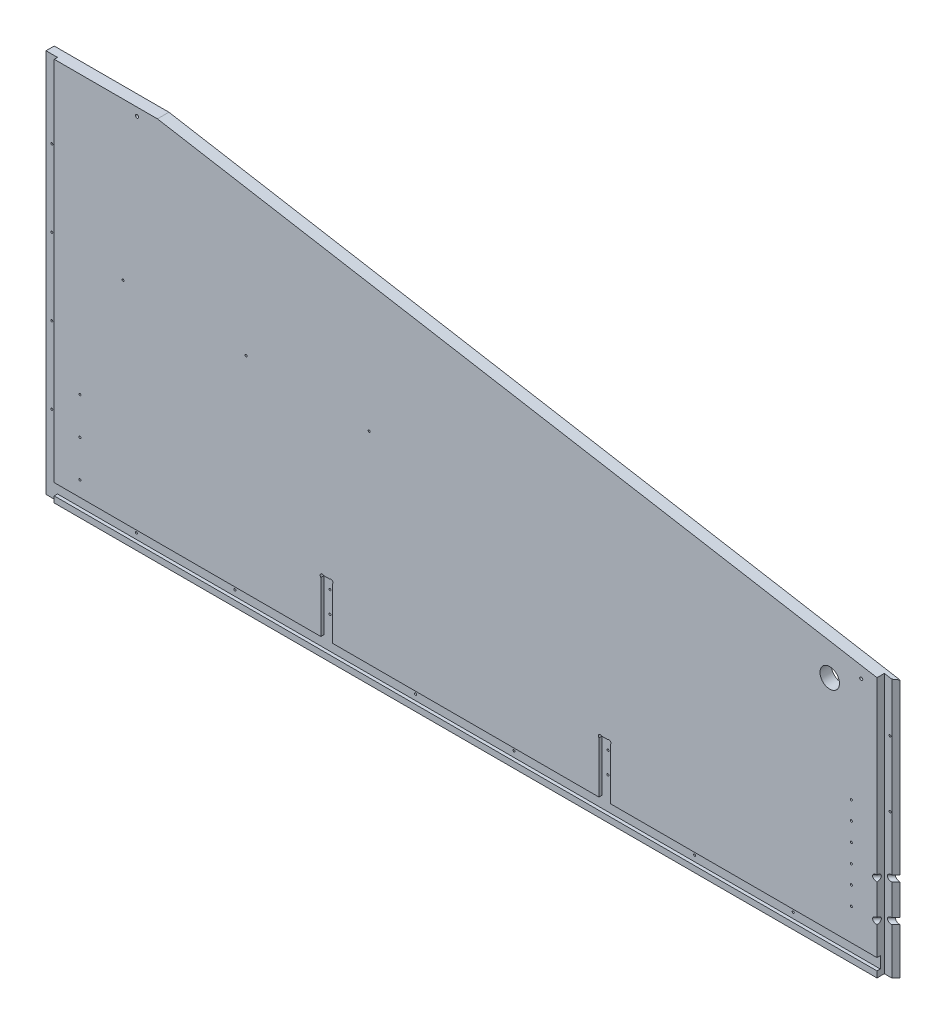
SolidWorks part; units mm, degrees
material "Maple"
ref_plane "Front Plane" through (0, 0, 0) normal (0, 0, 1) x (1, 0, 0)
ref_plane "Top Plane" through (0, 0, 0) normal (0, 1, 0) x (1, 0, 0)
ref_plane "Right Plane" through (0, 0, 0) normal (1, 0, 0) x (0, 0, -1)
sketch "Sketch1" plane through (0, 0, 0) normal (0, 0, 1) x (1, 0, 0)
  line L0 (8932.6508, -5243.5125) -> (10226.1458, -5243.5125)
  line L1 (9086.3208, -4722.0918) -> (10222.9708, -4853.7812)
  line L2 (8914.8708, -6342.0625) -> (10197.5708, -6342.0625)
  line L3 (8914.8708, -5808.6625) -> (10197.5708, -5808.6625)
  line L4 (8919.6333, -5253.0375) -> (10218.2083, -5253.0375)
  line L5 (9134.2633, -4656.1375) -> (9134.2633, -4638.3575)
  line L6 (9091.0833, -4638.3575) -> (9134.2633, -4638.3575)
  line L7 (9091.0833, -4567.2375) -> (9091.0833, -4638.3575)
  line L8 (9134.2633, -4656.1375) -> (9581.3033, -4656.1375)
  line L9 (9091.0833, -4567.2375) -> (9624.4833, -4567.2375)
  line L10 (9581.3033, -4656.1375) -> (9581.3033, -4638.3575)
  line L11 (9581.3033, -4638.3575) -> (9624.4833, -4638.3575)
  line L12 (9624.4833, -4567.2375) -> (9624.4833, -4638.3575)
  line L13 (8932.6508, -5225.7325) -> (9344.9775, -5225.7325)
  line L14 (8932.6508, -5256.2125) -> (8932.6508, -5243.5125)
  line L15 (8911.6958, -5256.2125) -> (8932.6508, -5256.2125)
  line L16 (8914.8708, -4722.0918) -> (9086.3208, -4722.0918)
  line L17 (8911.6958, -4715.5913) -> (8932.6508, -4715.5913)
  line L18 (8914.8708, -6342.0625) -> (8914.8708, -5808.6625)
  line L19 (12082.9917, -4722.0918) -> (10946.3417, -4853.7812)
  line L20 (12236.6617, -5243.5125) -> (10943.1667, -5243.5125)
  line L21 (10951.1042, -5253.0375) -> (12249.6792, -5253.0375)
  line L22 (10838.3917, -5656.2625) -> (11308.2917, -5656.2625)
  line L23 (10838.3917, -5719.7625) -> (11308.2917, -5719.7625)
  line L24 (10838.3917, -5742.5368) -> (11308.2917, -5742.5368)
  line L25 (10806.6417, -6342.0625) -> (11340.0417, -6342.0625)
  line L26 (10803.4667, -6335.7125) -> (11343.2167, -6335.7125)
  line L27 (10803.4667, -6317.9325) -> (11343.2167, -6317.9325)
  line L28 (10943.1667, -5225.7325) -> (11376.4483, -5225.7325)
  line L29 (11506.7292, -4754.5625) -> (10806.6417, -4827.5875)
  line L30 (11506.7292, -4567.2375) -> (11506.7292, -4754.5625)
  line L31 (10806.6417, -4567.2375) -> (10806.6417, -4827.5875)
  line L32 (10806.6417, -4567.2375) -> (11506.7292, -4567.2375)
  line L33 (10235.6708, -6329.3625) -> (10245.1958, -6329.3625)
  line L34 (10245.1958, -6329.3625) -> (10254.7208, -6278.5625)
  line L35 (10302.3458, -6329.3625) -> (10311.8708, -6278.5625)
  line L36 (10302.3458, -6329.3625) -> (10292.8208, -6329.3625)
  line L37 (10245.1958, -5821.3625) -> (10254.7208, -5872.1625)
  line L38 (10235.6708, -5821.3625) -> (10245.1958, -5821.3625)
  line L39 (10292.8208, -5821.3625) -> (10302.3458, -5821.3625)
  line L40 (10302.3458, -5821.3625) -> (10311.8708, -5872.1625)
  line L41 (10235.6708, -5821.3625) -> (10235.6708, -6329.3625)
  line L42 (10254.7208, -5872.1625) -> (10254.7208, -6278.5625)
  line L43 (10311.8708, -5872.1625) -> (10311.8708, -6278.5625)
  line L44 (10292.8208, -5821.3625) -> (10292.8208, -6329.3625)
  line L45 (8932.6508, -5225.7325) -> (8932.6508, -4715.5913)
  line L46 (8911.6958, -4715.5913) -> (8911.6958, -5256.2125)
  line L47 (8914.8708, -5248.275) -> (8914.8708, -4722.0918)
  line L48 (8919.6333, -5253.0375) -> (8914.8708, -5248.275)
  line L49 (8914.8708, -5145.0875) -> (8937.426, -5145.0875)
  line L50 (8914.8708, -5202.2375) -> (8937.426, -5202.2375)
  line L51 (10838.3917, -5656.2625) -> (10838.3917, -5719.7625)
  line L52 (10832.0417, -5736.1868) -> (10856.1717, -5736.1868)
  line L53 (10806.6417, -6342.0625) -> (10806.6417, -5818.7368)
  line L54 (10832.0417, -5649.9125) -> (10856.1717, -5649.9125)
  line L55 (10832.0417, -5726.1125) -> (10856.1717, -5726.1125)
  line L56 (10806.6417, -5818.7368) -> (10833.9015, -5818.7368)
  line L57 (10832.0417, -5806.0442) -> (10851.6815, -5806.0442)
  line L58 (10856.1717, -5801.5541) -> (10856.1717, -5736.1868)
  line L59 (10838.3917, -5814.2467) -> (10838.3917, -5742.5368)
  line L60 (10832.0417, -5806.0442) -> (10832.0417, -5736.1868)
  line L61 (10803.4667, -6317.9325) -> (10803.4667, -6335.7125)
  line L62 (10197.5708, -5808.6625) -> (10197.5708, -6342.0625)
  line L63 (9762.3842, -6348.4125) -> (9762.3842, -5802.3125)
  line L64 (9780.1642, -6348.4125) -> (9762.3842, -6348.4125)
  line L65 (9780.1642, -5802.3125) -> (9780.1642, -6348.4125)
  line L66 (9762.3842, -5802.3125) -> (9780.1642, -5802.3125)
  line L67 (9332.2775, -6348.4125) -> (9332.2775, -5802.3125)
  line L68 (9332.2775, -6348.4125) -> (9350.0575, -6348.4125)
  line L69 (9350.0575, -5802.3125) -> (9350.0575, -6348.4125)
  line L70 (9332.2775, -5802.3125) -> (9350.0575, -5802.3125)
  line L71 (9993.8374, -6061.075) -> (9993.8374, -6045.2418)
  line L72 (9998.5999, -6065.8375) -> (10014.4331, -6065.8375)
  line L73 (9998.5999, -6084.8875) -> (10014.4331, -6084.8875)
  line L74 (9993.8374, -6105.4832) -> (9993.8374, -6089.65)
  line L75 (9974.7874, -6105.4832) -> (9974.7874, -6089.65)
  line L76 (9954.1917, -6084.8875) -> (9970.0249, -6084.8875)
  line L77 (9974.7874, -6061.075) -> (9974.7874, -6045.2418)
  line L78 (9954.1917, -6065.8375) -> (9970.0249, -6065.8375)
  line L79 (10793.9417, -6237.2875) -> (10816.4969, -6237.2875)
  line L80 (10793.9417, -6294.4375) -> (10816.4969, -6294.4375)
  line L81 (10856.1717, -5649.9125) -> (10856.1717, -5726.1125)
  line L82 (10832.0417, -5726.1125) -> (10832.0417, -5649.9125)
  line L83 (10226.1458, -5225.7325) -> (10226.1458, -5243.5125)
  line L84 (10205.1908, -5257.8) -> (10205.1908, -4844.2499)
  line L85 (10230.9083, -4844.2499) -> (10230.9083, -5257.8)
  line L86 (10205.1908, -5257.8) -> (10230.9083, -5257.8)
  line L87 (10205.1908, -4844.2499) -> (10230.9083, -4844.2499)
  line L88 (10946.3417, -5176.8375) -> (10968.8969, -5176.8375)
  line L89 (9349.4676, -5141.9125) -> (9358.2674, -5141.9125)
  line L90 (10946.3417, -5119.6875) -> (10968.8969, -5119.6875)
  line L91 (9929.011, -4660.9635) -> (10066.0807, -4660.9635)
  line L92 (9929.011, -4678.7435) -> (10066.0807, -4678.7435)
  line L93 (10943.1667, -5225.7325) -> (10943.1667, -5243.5125)
  line L94 (10946.3417, -5248.275) -> (10951.1042, -5253.0375)
  line L95 (10946.3417, -5257.8063) -> (10946.3417, -4849.0188)
  line L96 (10964.1217, -5257.8) -> (10964.1217, -4844.2499)
  line L97 (10938.4042, -4844.2499) -> (10938.4042, -5257.8)
  line L98 (10938.4042, -5257.8) -> (10964.1217, -5257.8)
  line L99 (10964.1217, -4844.2499) -> (10938.4042, -4844.2499)
  line L100 (10344.8908, -4560.8875) -> (10369.0208, -4560.8875)
  line L101 (10344.8908, -4560.8875) -> (10369.0208, -4560.8875)
  line L102 (10800.2917, -4560.8875) -> (10824.4217, -4560.8875)
  line L103 (10200.4156, -5119.6875) -> (10222.9708, -5119.6875)
  line L104 (10200.4156, -5176.8375) -> (10222.9708, -5176.8375)
  line L105 (9344.9775, -5146.4026) -> (9344.9775, -5225.7325)
  line L106 (10344.8908, -4560.8875) -> (10344.8908, -4833.9375)
  line L107 (9792.8642, -5225.7325) -> (9792.8642, -5146.4026)
  line L108 (9362.7575, -5225.7325) -> (9775.0842, -5225.7325)
  line L109 (9680.3633, -4761.8396) -> (9680.3633, -4559.9604)
  line L110 (9656.2333, -4559.9604) -> (9680.3633, -4559.9604)
  line L111 (9656.2333, -4761.8396) -> (9680.3633, -4761.8396)
  line L112 (9656.2333, -4761.8396) -> (9656.2333, -4559.9604)
  line L113 (9779.5743, -5141.9125) -> (9788.374, -5141.9125)
  line L114 (10070.5708, -4665.4536) -> (10070.5708, -4674.2534)
  line L115 (9924.5208, -4674.2534) -> (9924.5208, -4665.4536)
  line L116 (12127.4417, -6188.3925) -> (12205.5015, -6188.3925)
  line L117 (12209.9917, -6170.6125) -> (12209.9917, -6183.9024)
  line L118 (9792.8642, -5225.7325) -> (10226.1458, -5225.7325)
  line L119 (9662.5833, -4754.5625) -> (10362.6708, -4827.5875)
  line L120 (9662.5833, -4567.2375) -> (9662.5833, -4754.5625)
  line L121 (10362.6708, -4567.2375) -> (10362.6708, -4827.5875)
  line L122 (9662.5833, -4567.2375) -> (10362.6708, -4567.2375)
  line L123 (10824.4217, -4833.9375) -> (10800.2917, -4833.9375)
  line L124 (10800.2917, -4833.9375) -> (10800.2917, -4560.8875)
  line L125 (10824.4217, -4560.8875) -> (10824.4217, -4833.9375)
  line L126 (10344.8908, -4833.9375) -> (10369.0208, -4833.9375)
  line L127 (10369.0208, -4833.9375) -> (10369.0208, -4560.8875)
  line L128 (10222.9708, -5248.275) -> (10218.2083, -5253.0375)
  line L129 (10222.9708, -5257.8063) -> (10222.9708, -4849.0188)
  line L130 (11734.6544, -5701.375) -> (11739.2301, -5701.375)
  line L131 (9362.7575, -5225.7325) -> (9362.7575, -5146.4026)
  line L132 (9775.0842, -5146.4026) -> (9775.0842, -5225.7325)
  line L133 (11761.3864, -5701.375) -> (11756.8282, -5701.375)
  line L134 (11734.6544, -5693.755) -> (11739.2301, -5693.755)
  line L135 (11761.4039, -5693.755) -> (11756.8282, -5693.755)
  line L136 (11734.6544, -5701.375) -> (11739.2301, -5701.375)
  line L137 (11744.3462, -5721.3024) -> (11744.3462, -5706.4179)
  line L138 (11751.7122, -5721.3024) -> (11751.7122, -5706.4179)
  line L139 (11740.0917, -6170.6125) -> (11740.0917, -6183.9024)
  line L140 (11689.2917, -6188.3925) -> (11822.6417, -6188.3925)
  line L141 (11689.2917, -6348.4093) -> (11689.2917, -6164.2657)
  line L142 (11689.2917, -6164.2657) -> (11746.4417, -6164.2657)
  line L143 (11746.4417, -6164.2657) -> (11746.4417, -6188.3925)
  line L144 (11689.2917, -6164.2657) -> (11746.4417, -6164.2657)
  line L145 (11340.0417, -5818.7368) -> (11340.0417, -6342.0625)
  line L146 (11290.5117, -5726.1125) -> (11314.6417, -5726.1125)
  line L147 (11290.5117, -5649.9125) -> (11290.5117, -5726.1125)
  line L148 (11340.0417, -5818.7368) -> (11312.7818, -5818.7368)
  line L149 (11314.6417, -5806.0442) -> (11295.0018, -5806.0442)
  line L150 (11290.5117, -5801.5541) -> (11290.5117, -5736.1868)
  line L151 (11308.2917, -5814.2467) -> (11308.2917, -5742.5368)
  line L152 (11314.6417, -5806.0442) -> (11314.6417, -5736.1868)
  line L153 (11290.5117, -5736.1868) -> (11314.6417, -5736.1868)
  line L154 (11848.0417, -6267.1325) -> (11962.3417, -6267.1325)
  line L155 (11962.3417, -6267.1325) -> (11962.3417, -6203.6325)
  line L156 (11343.2167, -6317.9325) -> (11343.2167, -6335.7125)
  line L157 (11365.4417, -5656.2625) -> (11365.4417, -5719.7625)
  line L158 (11365.4417, -5656.2625) -> (11479.7417, -5656.2625)
  line L159 (11778.1917, -6071.3937) -> (11802.3217, -6071.3937)
  line L160 (11314.6417, -5726.1125) -> (11314.6417, -5649.9125)
  line L161 (11314.6417, -5649.9125) -> (11290.5117, -5649.9125)
  line L162 (11308.2917, -5719.7625) -> (11308.2917, -5656.2625)
  line L163 (11689.2917, -6348.4093) -> (11713.4217, -6348.4093)
  line L164 (12203.6417, -6164.2657) -> (12260.7917, -6164.2657)
  line L165 (11713.4217, -6348.4093) -> (11713.4217, -6164.2657)
  line L166 (11695.6417, -6342.0625) -> (11695.6417, -6170.6125)
  line L167 (11695.6417, -6048.5337) -> (11699.4517, -6052.3437)
  line L168 (11822.6417, -6292.5325) -> (11822.6417, -6188.3925)
  line L169 (11695.6417, -6342.0625) -> (11695.6417, -6170.6125)
  line L170 (11848.0417, -6203.6325) -> (11962.3417, -6203.6325)
  line L171 (11848.0417, -6203.6325) -> (11848.0417, -6267.1325)
  line L172 (11987.7417, -6267.1325) -> (11987.7417, -6203.6325)
  line L173 (11784.5417, -6077.7437) -> (11784.5417, -6141.2438)
  line L174 (11517.8417, -5656.2625) -> (11632.1417, -5656.2625)
  line L175 (11632.1417, -5656.2625) -> (11632.1417, -5719.7625)
  line L176 (11632.1417, -5719.7625) -> (11517.8417, -5719.7625)
  line L177 (11517.8417, -5719.7625) -> (11517.8417, -5656.2625)
  line L178 (11692.4667, -6028.2137) -> (11692.4667, -6045.9937)
  line L179 (11695.6417, -5979.3188) -> (11718.1969, -5979.3188)
  line L180 (11695.6417, -5922.1687) -> (11718.1969, -5922.1687)
  line L181 (11821.0415, -5722.9375) -> (11821.0415, -5943.6)
  line L182 (11687.7042, -5651.5) -> (11701.9917, -5651.5)
  line L183 (11687.7042, -5651.5) -> (11687.7042, -6055.5251)
  line L184 (11687.7042, -6055.5251) -> (11701.9917, -6055.5251)
  line L185 (11701.9917, -6055.5251) -> (11701.9917, -5651.5)
  line L186 (11695.6417, -6055.2013) -> (11695.6417, -5649.595)
  line L187 (11695.6417, -5656.2625) -> (11695.6417, -6048.5337)
  line L188 (11695.6417, -6170.6125) -> (11740.0917, -6170.6125)
  line L189 (12203.6417, -6164.2657) -> (12203.6417, -6188.3925)
  line L190 (12254.4417, -6342.0625) -> (12254.4417, -6170.6125)
  line L191 (12129.0419, -5943.6) -> (12129.0419, -5722.9375)
  line L192 (12254.4417, -6048.5337) -> (12250.6317, -6052.3437)
  line L193 (12257.6167, -6045.9937) -> (12257.6167, -6028.2137)
  line L194 (12248.0917, -5651.5) -> (12262.3792, -5651.5)
  line L195 (12262.3792, -5651.5) -> (12262.3792, -6055.5251)
  line L196 (12262.3792, -6055.5251) -> (12248.0917, -6055.5251)
  line L197 (12248.0917, -6055.5251) -> (12248.0917, -5651.5)
  line L198 (12254.4417, -6141.2438) -> (12254.4417, -6077.7437)
  line L199 (12236.6617, -6164.2657) -> (12260.7917, -6164.2657)
  line L200 (12102.0417, -6267.1325) -> (11987.7417, -6267.1325)
  line L201 (11330.1865, -6237.2875) -> (11352.7417, -6237.2875)
  line L202 (11330.1865, -6294.4375) -> (11352.7417, -6294.4375)
  line L203 (11474.6617, -5851.8425) -> (11492.4417, -5851.8425)
  line L204 (11474.6617, -5808.6625) -> (11474.6617, -5851.8425)
  line L205 (11403.5417, -5808.6625) -> (11474.6617, -5808.6625)
  line L206 (11492.4417, -5851.8425) -> (11492.4417, -6298.8825)
  line L207 (11403.5417, -6342.0625) -> (11403.5417, -5808.6625)
  line L208 (11474.6617, -6298.8825) -> (11492.4417, -6298.8825)
  line L209 (11474.6617, -6342.0625) -> (11474.6617, -6298.8825)
  line L210 (11403.5417, -6342.0625) -> (11474.6617, -6342.0625)
  line L211 (11619.4417, -5851.8425) -> (11601.6617, -5851.8425)
  line L212 (11601.6617, -5808.6625) -> (11601.6617, -5851.8425)
  line L213 (11530.5417, -5808.6625) -> (11601.6617, -5808.6625)
  line L214 (11619.4417, -5851.8425) -> (11619.4417, -6298.8825)
  line L215 (11530.5417, -6342.0625) -> (11530.5417, -5808.6625)
  line L216 (11619.4417, -6298.8825) -> (11601.6617, -6298.8825)
  line L217 (11601.6617, -6342.0625) -> (11601.6617, -6298.8825)
  line L218 (11530.5417, -6342.0625) -> (11601.6617, -6342.0625)
  line L219 (11479.7417, -5719.7625) -> (11479.7417, -5656.2625)
  line L220 (11365.4417, -5719.7625) -> (11479.7417, -5719.7625)
  line L221 (11778.1917, -6147.5937) -> (11802.3217, -6147.5937)
  line L222 (11802.3217, -6071.3937) -> (11802.3217, -6147.5937)
  line L223 (11778.1917, -6147.5937) -> (11778.1917, -6071.3937)
  line L224 (12254.4417, -5922.1687) -> (12231.8865, -5922.1687)
  line L225 (12254.4417, -5979.3188) -> (12231.8865, -5979.3188)
  line L226 (12254.4417, -6055.2013) -> (12254.4417, -5649.595)
  line L227 (12254.4417, -6048.5337) -> (12254.4417, -5656.2625)
  line L228 (11841.6917, -5702.2873) -> (12108.3917, -5702.2873)
  line L229 (11822.6417, -6292.5325) -> (12127.4417, -6292.5325)
  line L230 (12127.4417, -6292.5325) -> (12127.4417, -6188.3925)
  line L231 (12254.4417, -6170.6125) -> (12209.9917, -6170.6125)
  line L232 (11695.6417, -6342.0625) -> (12254.4417, -6342.0625)
  line L233 (12236.6617, -6348.4093) -> (12260.7917, -6348.4093)
  line L234 (12260.7917, -6348.4093) -> (12260.7917, -6164.2657)
  line L235 (12236.6617, -6348.4093) -> (12236.6617, -6164.2657)
  line L236 (12102.0417, -6203.6325) -> (12102.0417, -6267.1325)
  line L237 (11987.7417, -6203.6325) -> (12102.0417, -6203.6325)
  line L238 (12236.6617, -6147.5937) -> (12236.6617, -6071.3937)
  line L239 (12203.6417, -6188.3925) -> (12260.7917, -6188.3925)
  line L240 (11098.7417, -4665.4536) -> (11098.7417, -4674.2534)
  line L241 (11394.2283, -5146.4026) -> (11394.2283, -5225.7325)
  line L242 (11376.4483, -5225.7325) -> (11376.4483, -5146.4026)
  line L243 (11394.2283, -5225.7325) -> (11806.555, -5225.7325)
  line L244 (11841.6917, -5964.2502) -> (12108.3917, -5964.2502)
  line L245 (12236.6617, -6147.5937) -> (12260.7917, -6147.5937)
  line L246 (12236.6617, -5256.2125) -> (12236.6617, -5243.5125)
  line L247 (12260.7917, -6147.5937) -> (12260.7917, -6071.3937)
  line L248 (12260.7917, -6071.3937) -> (12236.6617, -6071.3937)
  line L249 (12254.4417, -6077.7437) -> (11784.5417, -6077.7437)
  line L250 (11784.5417, -6141.2438) -> (12254.4417, -6141.2438)
  line L252 (12254.4417, -5656.2625) -> (11695.6417, -5656.2625)
  line L253 (11699.4517, -6052.3437) -> (12250.6317, -6052.3437)
  line L254 (11692.4667, -6045.9937) -> (12257.6167, -6045.9937)
  line L255 (11692.4667, -6028.2137) -> (12257.6167, -6028.2137)
  line L256 (11824.335, -5146.4026) -> (11824.335, -5225.7325)
  line L257 (11811.0451, -5141.9125) -> (11819.8449, -5141.9125)
  line L258 (11244.7917, -4674.2534) -> (11244.7917, -4665.4536)
  line L259 (11806.555, -5225.7325) -> (11806.555, -5146.4026)
  line L260 (11488.9492, -4761.8396) -> (11488.9492, -4559.9604)
  line L261 (11488.9492, -4559.9604) -> (11513.0792, -4559.9604)
  line L262 (11488.9492, -4761.8396) -> (11513.0792, -4761.8396)
  line L263 (11513.0792, -4761.8396) -> (11513.0792, -4559.9604)
  line L264 (11240.3015, -4660.9635) -> (11103.2318, -4660.9635)
  line L265 (11103.2318, -4678.7435) -> (11240.3015, -4678.7435)
  line L266 (12236.6617, -5225.7325) -> (12236.6617, -4715.5913)
  line L267 (12257.6167, -4715.5913) -> (12257.6167, -5256.2125)
  line L268 (12254.4417, -5248.275) -> (12254.4417, -4722.0918)
  line L269 (12236.6617, -5225.7325) -> (11824.335, -5225.7325)
  line L270 (12035.0492, -4656.1375) -> (12035.0492, -4638.3575)
  line L271 (12078.2292, -4638.3575) -> (12035.0492, -4638.3575)
  line L272 (12078.2292, -4567.2375) -> (12078.2292, -4638.3575)
  line L273 (12035.0492, -4656.1375) -> (11588.0092, -4656.1375)
  line L274 (11544.8292, -4567.2375) -> (12078.2292, -4567.2375)
  line L275 (11588.0092, -4656.1375) -> (11588.0092, -4638.3575)
  line L276 (11544.8292, -4638.3575) -> (11588.0092, -4638.3575)
  line L277 (11544.8292, -4567.2375) -> (11544.8292, -4638.3575)
  line L278 (12249.6792, -5253.0375) -> (12254.4417, -5248.275)
  line L280 (12257.6167, -5256.2125) -> (12236.6617, -5256.2125)
  line L281 (12231.8865, -5145.0875) -> (12254.4417, -5145.0875)
  line L282 (12231.8865, -5202.2375) -> (12254.4417, -5202.2375)
  line L283 (12236.6617, -4715.5913) -> (12257.6167, -4715.5913)
  line L284 (12082.9917, -4722.0918) -> (12254.4417, -4722.0918)
  line L285 (11380.9385, -5141.9125) -> (11389.7382, -5141.9125)
  circle A0 centre (8923.7608, -4778.9042) radius 1.5875
  circle A1 centre (9062.6598, -4736.3765) radius 2.3685
  circle A2 centre (9051.3958, -6281.7375) radius 22.225
  circle A3 centre (9083.1458, -6249.9875) radius 1.5875
  circle A4 centre (9083.1458, -6313.4875) radius 1.5875
  circle A5 centre (9019.6458, -6249.9875) radius 1.5875
  circle A6 centre (9019.6458, -6313.4875) radius 1.5875
  circle A7 centre (8972.3383, -5202.2375) radius 1.5875
  circle A8 centre (8923.7608, -5015.9708) radius 1.5875
  circle A9 centre (8923.7608, -5134.5042) radius 1.5875
  circle A10 centre (9054.5708, -5234.6225) radius 1.5875
  circle A11 centre (8923.7608, -4897.4375) radius 1.5875
  circle A12 centre (8972.3383, -5087.9375) radius 1.5875
  circle A13 centre (8972.3383, -5145.0875) radius 1.5875
  circle A14 centre (10847.2817, -5668.9625) radius 1.5875
  circle A15 centre (10847.2817, -5707.0625) radius 1.5875
  circle A16 centre (10847.2817, -5755.2368) radius 1.5875
  circle A17 centre (10851.4092, -6237.2875) radius 1.5875
  circle A18 centre (10851.4092, -6294.4375) radius 1.5875
  circle A19 centre (10847.2817, -5793.3442) radius 1.5875
  arc A20 (10833.9015, -5818.7368) -> (10838.3917, -5814.2467) centre (10836.1466, -5816.4918) ccw
  arc A21 (10851.6815, -5806.0442) -> (10856.1717, -5801.5541) centre (10853.9266, -5803.7992) ccw
  circle A22 centre (10882.8417, -6040.4375) radius 1.5875
  circle A23 centre (10882.8417, -6218.2375) radius 1.5875
  circle A24 centre (10882.8417, -5862.6375) radius 1.5875
  circle A25 centre (10908.2417, -6326.8225) radius 1.5875
  circle A26 centre (10908.2417, -6326.8225) radius 1.5875
  circle A27 centre (10851.4092, -6180.1375) radius 1.5875
  circle A28 centre (10815.5317, -4783.4231) radius 1.5875
  circle A29 centre (10815.5317, -4696.9488) radius 1.5875
  circle A30 centre (10815.5317, -4610.4746) radius 1.5875
  circle A31 centre (10979.1323, -4867.0082) radius 2.3685
  circle A32 centre (10190.1802, -4867.0082) radius 2.3685
  circle A33 centre (10955.2317, -4929.9812) radius 1.5875
  circle A34 centre (10955.2317, -5031.5812) radius 1.5875
  circle A35 centre (10214.0808, -4929.9812) radius 1.5875
  circle A36 centre (10214.0808, -5031.5812) radius 1.5875
  circle A37 centre (9341.1675, -6265.8625) radius 1.5875
  circle A38 centre (9771.2742, -5884.8625) radius 1.5875
  circle A39 centre (9771.2742, -6138.8625) radius 1.5875
  circle A40 centre (9771.2742, -6011.8625) radius 1.5875
  arc A41 (10036.2287, -6113.8083) -> (10051.3426, -6111.6033) centre (10042.9639, -6107.0732) ccw
  arc A42 (10051.3426, -6111.6033) -> (10051.3426, -6039.1217) centre (9984.3124, -6075.3625) ccw
  arc A43 (10051.3426, -6039.1217) -> (10036.2287, -6036.9167) centre (10042.9639, -6043.6518) ccw
  arc A44 (10034.5851, -6102.5431) -> (10034.5851, -6048.1819) centre (9984.3124, -6075.3625) ccw
  arc A45 (10034.5851, -6102.5431) -> (10036.2287, -6113.8083) centre (10042.9639, -6107.0732) ccw
  arc A46 (10036.2287, -6036.9167) -> (10034.5851, -6048.1819) centre (10042.9639, -6043.6518) ccw
  arc A47 (9945.8666, -6127.2787) -> (9948.0717, -6142.3927) centre (9952.6018, -6134.0139) ccw
  arc A48 (9948.0717, -6142.3927) -> (10020.5532, -6142.3927) centre (9984.3124, -6075.3625) ccw
  arc A49 (10020.5532, -6142.3927) -> (10022.7583, -6127.2787) centre (10016.0231, -6134.0139) ccw
  arc A50 (9957.1319, -6125.6352) -> (10011.493, -6125.6352) centre (9984.3124, -6075.3625) ccw
  arc A51 (9957.1319, -6125.6352) -> (9945.8666, -6127.2787) centre (9952.6018, -6134.0139) ccw
  arc A52 (10022.7583, -6127.2787) -> (10011.493, -6125.6352) centre (10016.0231, -6134.0139) ccw
  arc A53 (9932.3962, -6036.9167) -> (9917.2822, -6039.1217) centre (9925.661, -6043.6518) ccw
  arc A54 (9917.2822, -6039.1217) -> (9917.2822, -6111.6033) centre (9984.3124, -6075.3625) ccw
  arc A55 (9917.2822, -6111.6033) -> (9932.3962, -6113.8083) centre (9925.661, -6107.0732) ccw
  arc A56 (9934.0398, -6048.1819) -> (9934.0398, -6102.5431) centre (9984.3124, -6075.3625) ccw
  arc A57 (9934.0398, -6048.1819) -> (9932.3962, -6036.9167) centre (9925.661, -6043.6518) ccw
  arc A58 (9932.3962, -6113.8083) -> (9934.0398, -6102.5431) centre (9925.661, -6107.0732) ccw
  arc A59 (9945.8666, -6023.4463) -> (9957.1319, -6025.0898) centre (9952.6018, -6016.7111) ccw
  arc A60 (10011.493, -6025.0898) -> (10022.7583, -6023.4463) centre (10016.0231, -6016.7111) ccw
  arc A61 (10011.493, -6025.0898) -> (9957.1319, -6025.0898) centre (9984.3124, -6075.3625) ccw
  arc A62 (9948.0717, -6008.3323) -> (9945.8666, -6023.4463) centre (9952.6018, -6016.7111) ccw
  arc A63 (10020.5532, -6008.3323) -> (9948.0717, -6008.3323) centre (9984.3124, -6075.3625) ccw
  arc A64 (10022.7583, -6023.4463) -> (10020.5532, -6008.3323) centre (10016.0231, -6016.7111) ccw
  arc A65 (10005.0943, -6187.7574) -> (10096.7073, -6096.1443) centre (9984.3124, -6075.3625) ccw
  arc A66 (9993.8374, -6178.3911) -> (10005.0943, -6187.7574) centre (10003.3624, -6178.3911) ccw
  arc A67 (10001.6306, -6169.0249) -> (10077.9748, -6092.6807) centre (9984.3124, -6075.3625) ccw
  arc A68 (10087.3411, -6084.8875) -> (10077.9748, -6092.6807) centre (10087.3411, -6094.4125) ccw
  arc A69 (10001.6306, -6169.0249) -> (9993.8374, -6178.3911) centre (10003.3624, -6178.3911) ccw
  arc A70 (9963.5306, -6187.7574) -> (9974.7874, -6178.3911) centre (9965.2624, -6178.3911) ccw
  arc A71 (9871.9176, -6096.1443) -> (9963.5306, -6187.7574) centre (9984.3124, -6075.3625) ccw
  arc A72 (9881.2838, -6084.8875) -> (9871.9176, -6096.1443) centre (9881.2838, -6094.4125) ccw
  arc A73 (9890.65, -6092.6807) -> (9966.9943, -6169.0249) centre (9984.3124, -6075.3625) ccw
  arc A74 (9974.7874, -6178.3911) -> (9966.9943, -6169.0249) centre (9965.2624, -6178.3911) ccw
  arc A75 (9890.65, -6092.6807) -> (9881.2838, -6084.8875) centre (9881.2838, -6094.4125) ccw
  arc A76 (9871.9176, -6054.5807) -> (9881.2838, -6065.8375) centre (9881.2838, -6056.3125) ccw
  arc A77 (9963.5306, -5962.9676) -> (9871.9176, -6054.5807) centre (9984.3124, -6075.3625) ccw
  arc A78 (9974.7874, -5972.3339) -> (9963.5306, -5962.9676) centre (9965.2624, -5972.3339) ccw
  arc A79 (9966.9943, -5981.7001) -> (9890.65, -6058.0443) centre (9984.3124, -6075.3625) ccw
  arc A80 (9881.2838, -6065.8375) -> (9890.65, -6058.0443) centre (9881.2838, -6056.3125) ccw
  arc A81 (9966.9943, -5981.7001) -> (9974.7874, -5972.3339) centre (9965.2624, -5972.3339) ccw
  arc A82 (10077.9748, -6058.0443) -> (10087.3411, -6065.8375) centre (10087.3411, -6056.3125) ccw
  arc A83 (9993.8374, -5972.3339) -> (10001.6306, -5981.7001) centre (10003.3624, -5972.3339) ccw
  arc A84 (10077.9748, -6058.0443) -> (10001.6306, -5981.7001) centre (9984.3124, -6075.3625) ccw
  arc A85 (10087.3411, -6065.8375) -> (10096.7073, -6054.5807) centre (10087.3411, -6056.3125) ccw
  arc A86 (10096.7073, -6054.5807) -> (10005.0943, -5962.9676) centre (9984.3124, -6075.3625) ccw
  arc A87 (10005.0943, -5962.9676) -> (9993.8374, -5972.3339) centre (10003.3624, -5972.3339) ccw
  arc A88 (10014.4331, -6065.8375) -> (10018.7361, -6059.0339) centre (10014.4331, -6061.075) ccw
  arc A89 (10018.7361, -6059.0339) -> (10000.641, -6040.9388) centre (9984.3124, -6075.3625) ccw
  arc A90 (10000.641, -6040.9388) -> (9993.8374, -6045.2418) centre (9998.5999, -6045.2418) ccw
  arc A91 (9993.8374, -6061.075) -> (9998.5999, -6065.8375) centre (9998.5999, -6061.075) ccw
  arc A92 (9993.8374, -6105.4832) -> (10000.641, -6109.7862) centre (9998.5999, -6105.4832) ccw
  arc A93 (10000.641, -6109.7862) -> (10018.7361, -6091.6911) centre (9984.3124, -6075.3625) ccw
  arc A94 (10018.7361, -6091.6911) -> (10014.4331, -6084.8875) centre (10014.4331, -6089.65) ccw
  arc A95 (9998.5999, -6084.8875) -> (9993.8374, -6089.65) centre (9998.5999, -6089.65) ccw
  arc A96 (9954.1917, -6084.8875) -> (9949.8888, -6091.6911) centre (9954.1917, -6089.65) ccw
  arc A97 (9949.8888, -6091.6911) -> (9967.9839, -6109.7862) centre (9984.3124, -6075.3625) ccw
  arc A98 (9967.9839, -6109.7862) -> (9974.7874, -6105.4832) centre (9970.0249, -6105.4832) ccw
  arc A99 (9974.7874, -6089.65) -> (9970.0249, -6084.8875) centre (9970.0249, -6089.65) ccw
  arc A100 (9970.0249, -6065.8375) -> (9974.7874, -6061.075) centre (9970.0249, -6061.075) ccw
  arc A101 (9949.8888, -6059.0339) -> (9954.1917, -6065.8375) centre (9954.1917, -6061.075) ccw
  arc A102 (9967.9839, -6040.9388) -> (9949.8888, -6059.0339) centre (9984.3124, -6075.3625) ccw
  arc A103 (9974.7874, -6045.2418) -> (9967.9839, -6040.9388) centre (9970.0249, -6045.2418) ccw
  arc A104 (10096.7073, -6096.1443) -> (10087.3411, -6084.8875) centre (10087.3411, -6094.4125) ccw
  circle A105 centre (9771.2742, -6265.8625) radius 1.5875
  circle A106 centre (9341.1675, -5884.8625) radius 1.5875
  circle A107 centre (9341.1675, -6138.8625) radius 1.5875
  circle A108 centre (9341.1675, -6011.8625) radius 1.5875
  circle A109 centre (11037.2315, -4887.5494) radius 15.0812
  arc A110 (9349.4676, -5141.9125) -> (9344.9775, -5146.4026) centre (9347.2226, -5144.1576) ccw
  arc A111 (9362.7575, -5146.4026) -> (9358.2674, -5141.9125) centre (9360.5124, -5144.1576) ccw
  circle A112 centre (9946.7458, -4669.8535) radius 1.5875
  arc A113 (9924.5208, -4674.2534) -> (9929.011, -4678.7435) centre (9926.7659, -4676.4984) ccw
  circle A114 centre (11003.8092, -5176.8375) radius 1.5875
  circle A115 centre (11003.8092, -5119.6875) radius 1.5875
  circle A116 centre (10353.7808, -4696.9488) radius 1.5875
  circle A117 centre (10353.7808, -4610.4746) radius 1.5875
  circle A118 centre (10353.7808, -4783.4231) radius 1.5875
  circle A119 centre (11003.8092, -5062.5375) radius 1.5875
  circle A120 centre (9353.8675, -5160.9625) radius 1.5875
  circle A121 centre (9638.7708, -5234.6225) radius 1.5875
  circle A122 centre (9671.4733, -4724.1144) radius 1.5875
  circle A123 centre (9671.4733, -4661.3637) radius 1.5875
  circle A124 centre (9671.4733, -4598.6129) radius 1.5875
  arc A125 (9792.8642, -5146.4026) -> (9788.374, -5141.9125) centre (9790.6191, -5144.1576) ccw
  arc A126 (9779.5743, -5141.9125) -> (9775.0842, -5146.4026) centre (9777.3292, -5144.1576) ccw
  circle A127 centre (10048.3458, -4669.8535) radius 1.5875
  arc A128 (10070.5708, -4665.4536) -> (10066.0807, -4660.9635) centre (10068.3258, -4663.2086) ccw
  arc A129 (10066.0807, -4678.7435) -> (10070.5708, -4674.2534) centre (10068.3258, -4676.4984) ccw
  circle A130 centre (9997.5458, -4669.8535) radius 1.5875
  arc A131 (9929.011, -4660.9635) -> (9924.5208, -4665.4536) centre (9926.7659, -4663.2086) ccw
  circle A132 centre (10132.081, -4887.5494) radius 15.0812
  circle A133 centre (10165.5033, -5176.8375) radius 1.5875
  circle A134 centre (10165.5033, -5119.6875) radius 1.5875
  circle A135 centre (9486.3708, -5234.6225) radius 1.5875
  circle A136 centre (10165.5033, -5062.5375) radius 1.5875
  circle A137 centre (9206.9708, -5234.6225) radius 1.5875
  circle A138 centre (10070.5708, -5234.6225) radius 1.5875
  circle A139 centre (9918.1708, -5234.6225) radius 1.5875
  circle A140 centre (9783.9742, -5160.9625) radius 1.5875
  circle A141 centre (9783.9742, -5193.9825) radius 1.5875
  circle A142 centre (9353.8675, -5193.9825) radius 1.5875
  circle A143 centre (11073.3417, -6326.8225) radius 1.5875
  circle A144 centre (11073.3417, -6326.8225) radius 1.5875
  circle A145 centre (11295.2742, -6180.1375) radius 1.5875
  circle A146 centre (11295.2742, -6294.4375) radius 1.5875
  circle A147 centre (11295.2742, -6237.2875) radius 1.5875
  circle A148 centre (11975.0417, -5692.775) radius 3.4925
  circle A149 centre (11263.8417, -5862.6375) radius 1.5875
  arc A150 (11739.2301, -5701.375) -> (11744.3462, -5706.4179) centre (11748.0292, -5697.565) ccw
  arc A151 (11751.7122, -5706.4179) -> (11756.8282, -5701.375) centre (11748.0292, -5697.565) ccw
  arc A152 (11744.3462, -5721.3024) -> (11751.7122, -5721.3024) centre (11748.0292, -5725.505) ccw
  arc A153 (11734.6544, -5693.755) -> (11724.9787, -5697.565) centre (11730.5667, -5697.565) ccw
  arc A154 (11756.8282, -5693.755) -> (11739.2301, -5693.755) centre (11748.0292, -5697.565) ccw
  arc A155 (11724.9787, -5697.565) -> (11734.6544, -5701.375) centre (11730.5667, -5697.565) ccw
  arc A156 (11761.3864, -5701.375) -> (11771.0797, -5697.565) centre (11765.4842, -5697.565) ccw
  arc A157 (11771.0797, -5697.565) -> (11761.4039, -5693.755) centre (11765.4917, -5697.565) ccw
  arc A158 (11740.0917, -6183.9024) -> (11744.5818, -6188.3925) centre (11742.3367, -6186.1474) ccw
  arc A159 (12205.5015, -6188.3925) -> (12209.9917, -6183.9024) centre (12207.7466, -6186.1474) ccw
  circle A160 centre (11299.4017, -5793.3442) radius 1.5875
  arc A161 (11308.2917, -5814.2467) -> (11312.7818, -5818.7368) centre (11310.5367, -5816.4918) ccw
  arc A162 (11290.5117, -5801.5541) -> (11295.0018, -5806.0442) centre (11292.7567, -5803.7992) ccw
  circle A163 centre (11704.5317, -6314.149) radius 1.5875
  circle A164 centre (11748.9817, -6208.7125) radius 1.5875
  circle A165 centre (11263.8417, -6218.2375) radius 1.5875
  circle A166 centre (11263.8417, -6040.4375) radius 1.5875
  circle A167 centre (11238.4417, -6326.8225) radius 1.5875
  circle A168 centre (11238.4417, -6326.8225) radius 1.5875
  circle A169 centre (11299.4017, -5668.9625) radius 1.5875
  circle A170 centre (11299.4017, -5707.0625) radius 1.5875
  circle A171 centre (11726.7567, -6179.5025) radius 1.5875
  circle A172 centre (11704.5317, -6199.3198) radius 1.5875
  circle A173 centre (11748.9817, -6272.2125) radius 1.5875
  circle A174 centre (11704.5317, -6256.7344) radius 1.5875
  circle A175 centre (11299.4017, -5755.2368) radius 1.5875
  circle A176 centre (11913.4467, -6301.4225) radius 1.5875
  circle A177 centre (11790.2567, -6301.4225) radius 1.5875
  circle A178 centre (11793.4317, -6128.5437) radius 1.5875
  circle A179 centre (11753.1092, -5865.0188) radius 1.5875
  circle A180 centre (11809.9417, -6037.1038) radius 1.5875
  circle A181 centre (11809.9417, -6037.1038) radius 1.5875
  circle A182 centre (11753.1092, -5922.1687) radius 1.5875
  circle A183 centre (11975.0417, -5973.7625) radius 3.4925
  circle A184 centre (11975.0417, -6037.1038) radius 1.5875
  circle A185 centre (11753.1092, -5979.3188) radius 1.5875
  circle A186 centre (11975.0417, -6037.1038) radius 1.5875
  arc A187 (11841.6917, -5702.2873) -> (11821.0415, -5722.9375) centre (11841.6917, -5722.9375) ccw
  circle A188 centre (11811.5292, -5833.2687) radius 3.4925
  arc A189 (11821.0415, -5943.6) -> (11841.6917, -5964.2502) centre (11841.6917, -5943.6) ccw
  circle A190 centre (12196.9742, -5865.0188) radius 1.5875
  arc A191 (12129.0419, -5722.9375) -> (12108.3917, -5702.2873) centre (12108.3917, -5722.9375) ccw
  circle A192 centre (12036.6367, -6301.4225) radius 1.5875
  circle A193 centre (12159.8267, -6301.4225) radius 1.5875
  circle A194 centre (12138.5542, -5833.2687) radius 3.4925
  circle A195 centre (12197.2917, -5761.0375) radius 15.0812
  circle A196 centre (11793.4317, -6090.4437) radius 1.5875
  circle A197 centre (12196.9742, -5922.1687) radius 1.5875
  arc A198 (12108.3917, -5964.2502) -> (12129.0419, -5943.6) centre (12108.3917, -5943.6) ccw
  circle A199 centre (12196.9742, -5979.3188) radius 1.5875
  circle A200 centre (12201.1017, -6272.2125) radius 1.5875
  circle A201 centre (12245.5517, -6314.149) radius 1.5875
  circle A202 centre (12245.5517, -6256.7344) radius 1.5875
  circle A203 centre (12201.1017, -6208.7125) radius 1.5875
  circle A204 centre (12223.3267, -6179.5025) radius 1.5875
  circle A205 centre (12245.5517, -6199.3198) radius 1.5875
  circle A206 centre (11171.7667, -4669.8535) radius 1.5875
  circle A207 centre (11222.5667, -4669.8535) radius 1.5875
  arc A208 (11240.3015, -4678.7435) -> (11244.7917, -4674.2534) centre (11242.5466, -4676.4984) ccw
  circle A209 centre (11385.3383, -5193.9825) radius 1.5875
  circle A210 centre (12106.6527, -4736.3765) radius 2.3685
  circle A211 centre (12140.1417, -6037.1038) radius 1.5875
  circle A212 centre (12140.1417, -6037.1038) radius 1.5875
  circle A213 centre (12245.5517, -6090.4437) radius 1.5875
  circle A214 centre (12245.5517, -6128.5437) radius 1.5875
  circle A215 centre (11385.3383, -5160.9625) radius 1.5875
  arc A216 (11824.335, -5146.4026) -> (11819.8449, -5141.9125) centre (11822.0899, -5144.1576) ccw
  arc A217 (11811.0451, -5141.9125) -> (11806.555, -5146.4026) centre (11808.8001, -5144.1576) ccw
  circle A218 centre (11815.445, -5193.9825) radius 1.5875
  circle A219 centre (11815.445, -5160.9625) radius 1.5875
  circle A220 centre (11530.5417, -5234.6225) radius 1.5875
  circle A221 centre (11962.3417, -5234.6225) radius 1.5875
  arc A222 (11244.7917, -4665.4536) -> (11240.3015, -4660.9635) centre (11242.5466, -4663.2086) ccw
  circle A223 centre (11682.9417, -5234.6225) radius 1.5875
  circle A224 centre (11497.8392, -4724.1144) radius 1.5875
  circle A225 centre (11497.8392, -4661.3637) radius 1.5875
  circle A226 centre (11497.8392, -4598.6129) radius 1.5875
  circle A227 centre (11120.9667, -4669.8535) radius 1.5875
  arc A228 (11103.2318, -4660.9635) -> (11098.7417, -4665.4536) centre (11100.9867, -4663.2086) ccw
  arc A229 (11098.7417, -4674.2534) -> (11103.2318, -4678.7435) centre (11100.9867, -4676.4984) ccw
  circle A230 centre (12196.9742, -5202.2375) radius 1.5875
  circle A231 centre (12245.5517, -5015.9708) radius 1.5875
  circle A232 centre (12245.5517, -5134.5042) radius 1.5875
  circle A233 centre (12114.7417, -5234.6225) radius 1.5875
  circle A234 centre (12245.5517, -4897.4375) radius 1.5875
  circle A235 centre (12245.5517, -4778.9042) radius 1.5875
  circle A236 centre (12196.9742, -5087.9375) radius 1.5875
  circle A237 centre (12196.9742, -5145.0875) radius 1.5875
  circle A238 centre (11098.7417, -5234.6225) radius 1.5875
  circle A239 centre (11251.1417, -5234.6225) radius 1.5875
  arc A240 (11380.9385, -5141.9125) -> (11376.4483, -5146.4026) centre (11378.6934, -5144.1576) ccw
  arc A241 (11394.2283, -5146.4026) -> (11389.7382, -5141.9125) centre (11391.9833, -5144.1576) ccw
sketch "CabSideRight_Outline" plane through (0, 0, 0) normal (0, 0, 1) x (1, 0, 0)
  line L0 (9092.2345, -4658.6775) -> (10222.9708, -4853.7812)
  line L1 (10222.9708, -4853.7812) -> (10222.9708, -5253.0375)
  line L3 (10222.9708, -5253.0375) -> (8914.8708, -5253.0375)
  line L5 (8914.8708, -5253.0375) -> (8914.8708, -4658.6775)
  line L6 (8914.8708, -4658.6775) -> (9092.2345, -4658.6775)
  dimension "SideRight_Lendgth" = 1308.1
  dimension "SideRight_Front" = 399.2562
  dimension "SideRight_BackHeight" = 594.36
  dimension "SideRight_SlopeLength" = 1147.445
extrude "CabSideRight_Thickness" add sketch "CabSideRight_Outline" against normal blind 17.78
sketch "CabSideRight_LedgeCuts" plane through (0, 0, 0) normal (0, 0, 1) x (1, 0, 0)
  line L0 (8932.6508, -4658.6775) -> (8914.8708, -4658.6775)
  line L1 (8914.8708, -4658.6775) -> (8914.8708, -5253.0375)
  line L2 (8914.8708, -5253.0375) -> (8932.6508, -5253.0375)
  line L3 (8932.6508, -5253.0375) -> (8932.6508, -5243.5125)
  line L4 (8932.6508, -5243.5125) -> (10222.9708, -5243.5125)
  line L5 (10222.9708, -5243.5125) -> (10222.9708, -5225.7325)
  line L6 (10222.9708, -5225.7325) -> (9792.8642, -5225.7325)
  line L7 (9792.8642, -5225.7325) -> (9792.8642, -5141.9125)
  line L8 (10222.9708, -5253.0375) -> (10222.9708, -4853.7812) construction
  line L9 (9792.8642, -5141.9125) -> (9775.0842, -5141.9125)
  line L11 (9775.0842, -5141.9125) -> (9775.0842, -5225.7325)
  line L12 (9775.0842, -5225.7325) -> (9362.7575, -5225.7325)
  line L13 (9362.7575, -5225.7325) -> (9362.7575, -5141.9125)
  line L15 (9362.7575, -5141.9125) -> (9344.9775, -5141.9125)
  line L17 (9344.9775, -5141.9125) -> (9344.9775, -5225.7325)
  line L18 (9344.9775, -5225.7325) -> (8932.6508, -5225.7325)
  line L19 (8932.6508, -5225.7325) -> (8932.6508, -4658.6775)
  line L20 (9092.2345, -4658.6775) -> (8914.8708, -4658.6775) construction
  line L21 (8914.8708, -5253.0375) -> (10222.9708, -5253.0375) construction
  dimension "BackThickness_2" = 17.78
  dimension "BackThickness_1" = 17.78
  dimension "BraceThickness_1" = 17.78
  dimension "BraceThickness_2" = 17.78
  dimension "BottomThickness" = 17.78
extrude "LedgeCuts_Depth" cut sketch "CabSideRight_LedgeCuts" against normal blind 5.08
sketch "Sketch9" plane through (0, 0, 0) normal (0, 0, 1) x (1, 0, 0)
  line L0 (9344.9775, -5141.9125) -> (9347.2226, -5144.1576) construction
  line L1 (9344.9775, -5141.9125) -> (9344.9775, -5225.7325) construction
  line L2 (9362.7575, -5141.9125) -> (9360.5124, -5144.1576) construction
  line L3 (9362.7575, -5225.7325) -> (9362.7575, -5141.9125) construction
  line L4 (9775.0842, -5141.9125) -> (9777.3292, -5144.1576) construction
  line L5 (9792.8642, -5141.9125) -> (9790.6191, -5144.1576) construction
  line L6 (9775.0842, -5141.9125) -> (9775.0842, -5225.7325) construction
  line L8 (9792.8642, -5225.7325) -> (9792.8642, -5141.9125) construction
  circle A0 centre (9347.2226, -5144.1576) radius 3.302
  circle A1 centre (9360.5124, -5144.1576) radius 3.175
  circle A2 centre (9777.3292, -5144.1576) radius 3.175
  circle A3 centre (9790.6191, -5144.1576) radius 3.175
  dimension "D1" = 45
  dimension "D2" = 3.175
  dimension "D3" = 45
  dimension "D4" = 3.175
  dimension "D5" = 45
  dimension "D6" = 3.175
  dimension "D7" = 3.175
  dimension "D8" = 45
extrude "Cut-Extrude4" cut sketch "Sketch9" against normal blind 5.08
sketch "Sketch10" plane through (0, 0, 0) normal (0, 0, 1) x (1, 0, 0)
  circle A0 centre (10132.081, -4887.5494) radius 15.0813
  circle A1 centre (10165.516, -5148.2625) radius 1.5875
  circle A2 centre (8923.7608, -4778.9042) radius 1.5875
  circle A3 centre (8923.7608, -4897.4375) radius 1.5875
  circle A4 centre (8923.7608, -5015.9708) radius 1.5875
  circle A5 centre (8923.7608, -5134.5042) radius 1.5875
  circle A6 centre (9054.5708, -5234.6225) radius 1.5875
  circle A7 centre (9206.9708, -5234.6225) radius 1.5875
  circle A8 centre (9353.8675, -5193.9825) radius 1.5875
  circle A9 centre (9353.8675, -5160.9625) radius 1.5875
  circle A10 centre (9486.3708, -5234.6225) radius 1.5875
  circle A11 centre (9638.7708, -5234.6225) radius 1.5875
  circle A12 centre (9783.9742, -5193.9825) radius 1.5875
  circle A13 centre (9783.9742, -5160.9625) radius 1.5875
  circle A14 centre (9918.1708, -5234.6225) radius 1.5875
  circle A15 centre (10070.5708, -5234.6225) radius 1.5875
  circle A16 centre (10214.0808, -5031.5812) radius 1.5875
  circle A17 centre (10214.0808, -4929.9812) radius 1.5875
  circle A18 centre (10165.516, -5091.1125) radius 1.5875
  circle A19 centre (8972.3383, -5087.9375) radius 1.5875
  circle A20 centre (8972.3383, -5145.0875) radius 1.5875
  circle A21 centre (8972.3383, -5202.2375) radius 1.5875
  circle A22 centre (10165.5033, -5176.8375) radius 1.5875
  circle A23 centre (10165.5033, -5119.6875) radius 1.5875
  circle A24 centre (10165.5033, -5062.5375) radius 1.5875
  circle A25 centre (10165.516, -5033.9625) radius 1.5875
extrude "Cut-Extrude5" cut sketch "Sketch10" against normal up to surface (17.78 mm away) up to face at (9473.5836, -4935.4422, -17.78)
sketch "FrontLedgeCut" plane through (0, 0, 0) normal (0, 0, 1) x (1, 0, 0)
  line L0 (10205.1908, -5253.0375) -> (10222.9708, -5253.0375)
  line L1 (10222.9708, -5253.0375) -> (10222.9708, -4850.7134)
  line L2 (10222.9708, -4850.7134) -> (10205.1908, -4850.7134)
  line L3 (10205.1908, -4850.7134) -> (10205.1908, -5253.0375)
  line L4 (8932.6508, -5253.0375) -> (10222.9708, -5253.0375) construction
  line L5 (10222.9708, -4853.7812) -> (9092.2345, -4658.6775) construction
  dimension "FrontThickness" = 17.78
extrude "FrontLedgeCut_Thickness" cut sketch "FrontLedgeCut" against normal blind 11.43
sketch "FrontBevelAngleCut" plane through (0, -5253.0375, 0) normal (0, -1, 0) x (1, 0, 0)
  line L0 (10205.1908, 0) -> (10222.9708, 0) construction
  line L1 (10222.9708, -17.78) -> (10222.9708, 0) construction
  line L2 (10222.9708, -11.43) -> (10229.3208, -11.43)
  line L3 (10222.9708, -11.43) -> (10216.6208, -11.43)
  line L5 (10229.3208, -11.43) -> (10222.9708, -17.78)
  line L6 (10222.9708, -17.78) -> (10216.6208, -11.43)
  dimension "FrontBevel_Thickness" = 17.78
  dimension "FrontBevel_Depth" = 17.78
  dimension "D3" = 45
  dimension "D4" = 6.35
extrude "Cut-Extrude8" cut sketch "FrontBevelAngleCut" against normal up to surface (594.36 mm away) up to face at (8979.9187, -4658.6775, -7.62)
sketch "Sketch15" plane through (0, 0, -17.78) normal (0, 0, -1) x (-1, 0, 0)
  line L0 (-10183.157, -4864.8061) -> (-10178.4639, -4863.9963) construction
  line L1 (-10182.7521, -4867.1526) -> (-10183.5619, -4862.4595) construction
  line L2 (-10178.8688, -4861.6497) -> (-10178.059, -4866.3429) construction
  line L3 (-9063.0586, -4671.5378) -> (-9058.3654, -4670.728) construction
  line L4 (-9062.6537, -4673.8844) -> (-9063.4634, -4669.1913) construction
  line L5 (-9058.7703, -4668.3815) -> (-9057.9605, -4673.0746) construction
  circle A0 centre (-10180.8105, -4864.4012) radius 2.3812
  circle A1 centre (-9060.712, -4671.1329) radius 2.3812
extrude "Cut-Extrude9" cut sketch "Sketch15" against normal up to surface (17.78 mm away) up to face at (10167.0908, -5062.5375, 0)
sketch "Sketch16" plane through (0, 0, 0) normal (0, 0, 1) x (1, 0, 0)
  circle A0 centre (9038.9923, -4901.4921) radius 1.5875
  circle A1 centre (9229.4035, -4907.3097) radius 1.5875
  circle A2 centre (9419.8146, -4913.1273) radius 1.5875
extrude "Cut-Extrude10" cut sketch "Sketch16" against normal blind 12.7
sketch "Sketch17" plane through (5086.5119, 0, -5086.5119) normal (-0.7071, 0, 0.7071) x (0.7071, 0, 0.7071)
  circle A0 centre (7216.1596, -5119.6875) radius 4.7625
  circle A1 centre (7216.1596, -5176.8375) radius 4.7625
extrude "Cut-Extrude11" cut sketch "Sketch17" against normal blind 76.2
